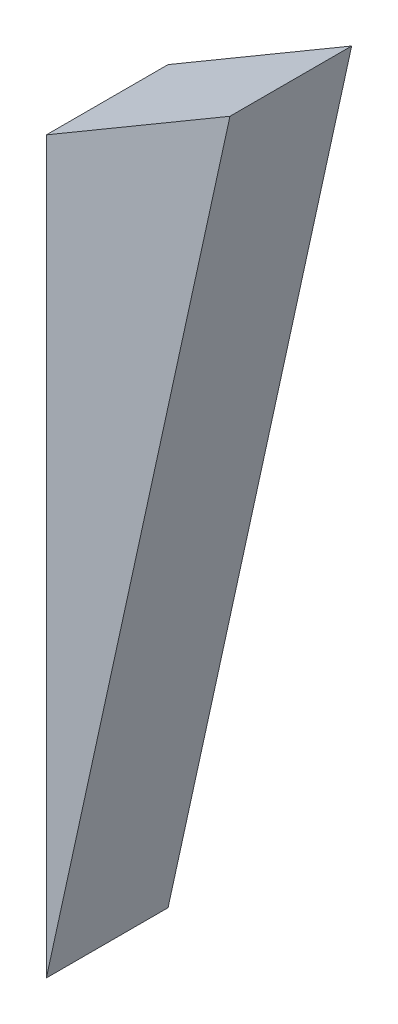
SolidWorks part; units mm, degrees
ref_plane "Front Plane" through (0, 0, 0) normal (0, 0, 1) x (1, 0, 0)
ref_plane "Top Plane" through (0, 0, 0) normal (0, 1, 0) x (1, 0, 0)
ref_plane "Right Plane" through (0, 0, 0) normal (1, 0, 0) x (0, 0, -1)
sketch "Sketch1" plane through (0, 0, 0) normal (0, 0, 1) x (1, 0, 0)
  line L0 (0, 0) -> (0, -12)
  line L1 (0, -12) -> (3.0175, 1.7733)
  line L2 (3.0175, 1.7733) -> (0, 0)
  dimension "D1" = 12
  dimension "D2" = 14.1
  dimension "D3" = 3.5
extrude "Boss-Extrude1" add sketch "Sketch1" along normal blind 2
